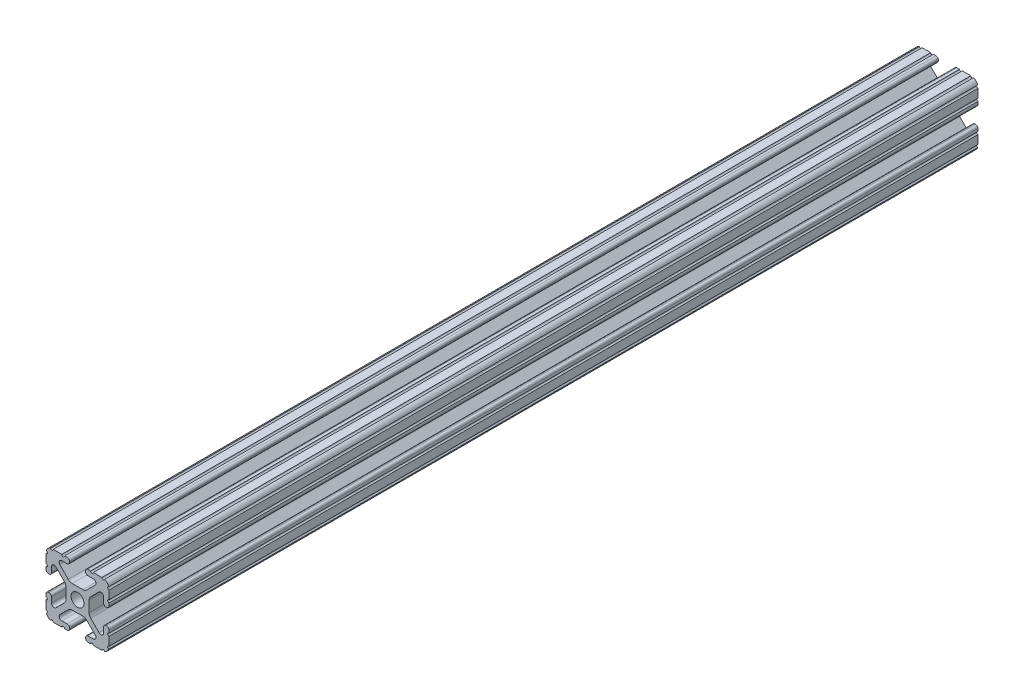
SolidWorks part; units mm, degrees
ref_plane "Front Plane" through (0, 0, 0) normal (0, 0, 1) x (1, 0, 0)
ref_plane "Top Plane" through (0, 0, 0) normal (0, 1, 0) x (1, 0, 0)
ref_plane "Right Plane" through (0, 0, 0) normal (1, 0, 0) x (0, 0, -1)
sketch "Sketch2" plane through (0, 0, 0) normal (0, 0, 1) x (1, 0, 0)
  line L0 (0, 12.7) -> (0, -12.7) construction
  line L1 (-12.7, 0) -> (12.7, 0) construction
  line L2 (3.2512, -12.7) -> (12.7, -12.7)
  line L3 (12.7, -12.7) -> (12.7, -3.2512)
  line L4 (3.2512, -12.7) -> (3.2512, -10.4902)
  line L5 (3.2512, -10.4902) -> (8.9276, -10.4902)
  line L6 (8.9276, -10.4902) -> (3.0856, -4.6482)
  line L7 (0, 0) -> (12.7, -12.7) construction
  line L8 (12.7, -3.2512) -> (10.4902, -3.2512)
  line L9 (10.4902, -3.2512) -> (10.4902, -8.9276)
  line L10 (10.4902, -8.9276) -> (4.6482, -3.0856)
  circle A0 centre (0, 0) radius 2.6035
  arc A1 (6.3485, -10.4902) -> (7.1039, -8.6665) centre (6.3485, -9.4219) ccw construction
  point P8 (0, -4.6482)
  dimension "Center Hole Diameter" = 5.207
  dimension "Rail Height" = 25.4
  dimension "Rail Width" = 25.4
  dimension "T-Slot Width" = 6.5024
  dimension "Slot Inner Width" = 14.8336
  dimension "Thickness" = 2.2098
  dimension "Slot Depth" = 5.842
  dimension "D1" = 2.2098
sketch "Sketch3" plane through (0, 0, 0) normal (1, 0, 0) x (0, 0, -1)
  line L0 (-76.2, -12.7) -> (76.2, -12.7) construction
  line L1 (-68.58, 0) -> (68.58, 0) construction
  dimension "Length" = 152.4
  dimension "D1" = 137.16
sketch "Sketch4" plane through (0, 0, 0) normal (0, 0, 1) x (1, 0, 0)
  line L0 (4.1904, -12.7) -> (10.1173, -12.7)
  line L1 (3.2512, -12.7) -> (12.7, -12.7) construction
  line L2 (3.2512, -12.7) -> (3.2512, -10.4902) construction
  line L3 (3.2512, -10.4902) -> (8.9276, -10.4902) construction
  line L4 (3.2512, -11.4294) -> (3.2512, -11.7608)
  line L5 (4.1904, -10.4902) -> (6.3485, -10.4902)
  line L6 (0, -4.6482) -> (2.164, -4.6482)
  line L7 (8.9276, -10.4902) -> (3.0856, -4.6482) construction
  line L8 (3.7373, -5.2999) -> (7.1039, -8.6665)
  line L9 (12.7, -12.7) -> (12.7, -3.2512) construction
  line L10 (10.4902, -8.9276) -> (4.6482, -3.0856) construction
  line L11 (10.4902, -3.2512) -> (10.4902, -8.9276) construction
  line L12 (10.4902, -6.3485) -> (10.4902, -4.1904)
  line L13 (12.7, -3.2512) -> (10.4902, -3.2512) construction
  line L14 (11.4294, -3.2512) -> (11.7608, -3.2512)
  line L15 (12.7, -4.1904) -> (12.7, -10.1173)
  line L16 (8.6665, -7.1039) -> (5.2999, -3.7373)
  line L17 (4.6482, 0) -> (4.6482, -2.164)
  line L18 (-12.7, 0) -> (12.7, 0) construction
  line L19 (0, -4.6482) -> (0, -2.6035)
  line L20 (0, 12.7) -> (0, -12.7) construction
  line L21 (4.6482, 0) -> (2.6035, 0)
  arc A0 (3.2512, -11.7608) -> (4.1904, -12.7) centre (4.1904, -11.7608) ccw
  arc A2 (3.2512, -11.4294) -> (4.1904, -10.4902) centre (4.1904, -11.4294) cw
  arc A3 (6.3485, -10.4902) -> (7.1039, -8.6665) centre (6.3485, -9.4219) ccw
  arc A4 (2.164, -4.6482) -> (3.7373, -5.2999) centre (2.164, -6.8732) cw
  arc A5 (10.1173, -12.7) -> (12.7, -10.1173) centre (10.1173, -10.1173) ccw
  arc A6 (8.6665, -7.1039) -> (10.4902, -6.3485) centre (9.4219, -6.3485) ccw
  arc A7 (10.4902, -4.1904) -> (11.4294, -3.2512) centre (11.4294, -4.1904) cw
  arc A8 (11.7608, -3.2512) -> (12.7, -4.1904) centre (11.7608, -4.1904) cw
  arc A9 (5.2999, -3.7373) -> (4.6482, -2.164) centre (6.8732, -2.164) cw
  circle A10 centre (0, 0) radius 2.6035 construction
  arc A11 (0, -2.6035) -> (2.6035, 0) centre (0, 0) ccw
  dimension "D1" = 2.5827
  dimension "D2" = 2.225
  dimension "D3" = 0.9392
extrude "Boss-Extrude1" add sketch "Sketch4" along normal mid plane 350
sketch "Sketch5" plane through (0, 0, 0) normal (0, 0, 1) x (1, 0, 0)
  line L0 (3.2512, -12.7) -> (12.7, -12.7) construction
  line L1 (4.1904, -10.4902) -> (6.3485, -10.4902) construction
  line L3 (0, 0) -> (12.7, -12.7) construction
  line L4 (6.3485, -10.4902) -> (6.3485, -12.7) construction
  line L5 (8.9276, -10.4902) -> (3.0856, -4.6482) construction
  circle A0 centre (10.3562, -12.7) radius 0.5524
  circle A1 centre (5.796, -12.7) radius 0.5524
  circle A2 centre (12.7, -10.3562) radius 0.5524
  circle A3 centre (12.7, -5.796) radius 0.5524
  point P10 (5.2694, -10.4902)
  point P12 (9.4219, -6.3485)
  dimension "D1" = 1.1049
extrude "Cut-Extrude1" cut sketch "Sketch5" against normal through all both and the other way through all
mirror "Mirror1" about plane through (0, 0, 0) normal (1, 0, 0) of bodies 137 134
mirror "Mirror2" about plane through (0, 0, 0) normal (0, 1, 0) of bodies 135
sketch "Sketch6" plane through (0, 0, 0) normal (0, 1, 0) x (1, 0, 0)
  line L0 (0, 175) -> (0, 162.3) construction
  line L1 (0, -175) -> (0, -162.3) construction
  line L4 (2.164, 175) -> (-2.164, 175)
  line L5 (-2.164, 175) -> (-2.164, -175)
  line L6 (-2.164, -175) -> (2.164, -175)
  line L7 (2.164, -175) -> (2.164, 175)
  line L8 (2.164, 175) -> (-2.164, 175) construction
  line L9 (-2.164, 175) -> (-2.164, -175) construction
  line L10 (-2.164, -175) -> (2.164, -175) construction
  line L11 (2.164, -175) -> (2.164, 175) construction
  circle A0 centre (0, -162.3) radius 2.555
  circle A1 centre (0, 162.3) radius 2.555
  dimension "D2" = 12.7
  dimension "D3" = 5.11
  dimension "D4" = 324.6
  dimension "D1" = 0
extrude "Cut-Extrude2" cut sketch "Sketch6" against normal through all both and the other way through all
equation "\"D1@Boss-Extrude1\"=350"
equation "\"D1@Sketch2\"=\"Thickness@Sketch2\""
equation "\"D2@Sketch4\"=\"Slot Inner Width@Sketch2\"*0.15"
equation "\"D1@Sketch4\"=\"D3@Sketch4\"*2.75"
equation "\"D3@Sketch4\"=\"Thickness@Sketch2\"*0.425"
equation "\"D1@Sketch5\"=\"Thickness@Sketch2\"*0.5"
equation "\"D1@Sketch3\"=\"Length@Sketch3\"*0.9"
